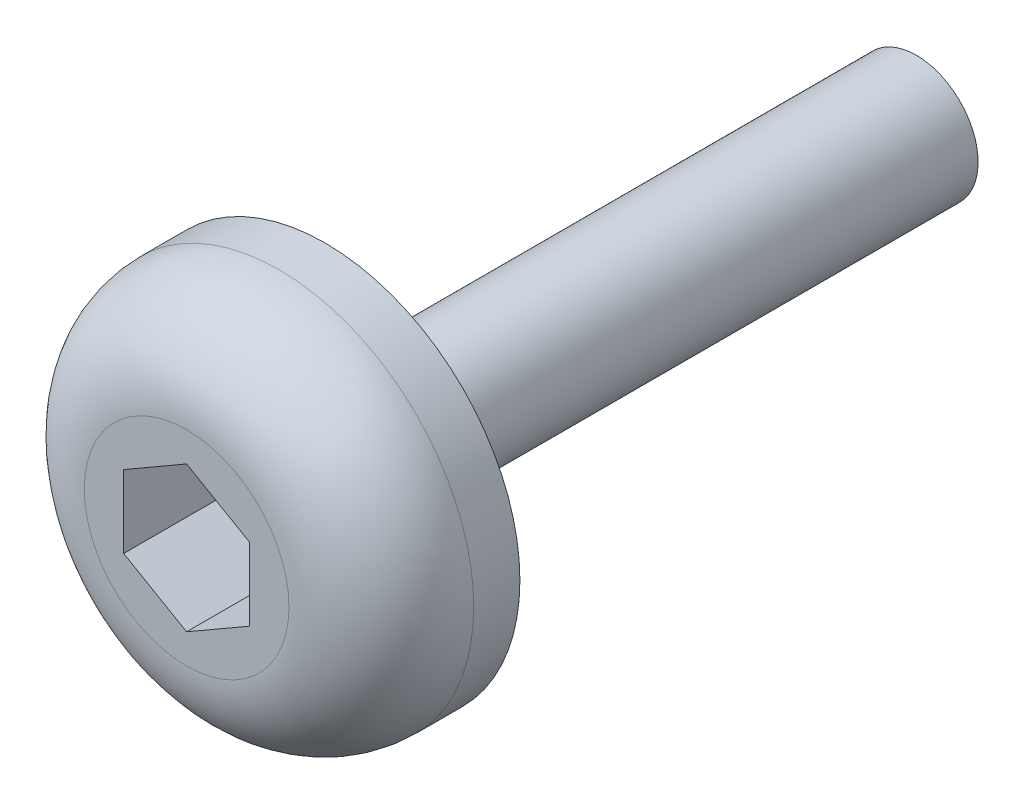
SolidWorks part; units mm, degrees
ref_plane "Front Plane" through (0, 0, 0) normal (0, 0, 1) x (1, 0, 0)
ref_plane "Top Plane" through (0, 0, 0) normal (0, 1, 0) x (1, 0, 0)
ref_plane "Right Plane" through (0, 0, 0) normal (1, 0, 0) x (0, 0, -1)
sketch "Sketch1" plane through (0, 0, 0) normal (0, 0, 1) x (1, 0, 0)
  circle A0 centre (0, 0) radius 5.3543
extrude "Boss-Extrude1" add sketch "Sketch1" along normal blind 3.81
fillet "Fillet1" radius 2.54 1 edges at (5.3543, 0, 3.81)
sketch "Sketch2" plane through (0, 0, 3.81) normal (0, 0, 1) x (1, 0, 0)
  line L1 (0, 1.9983) -> (-1.7306, 0.9992)
  line L2 (-1.7306, 0.9992) -> (-1.7306, -0.9992)
  line L3 (-1.7306, -0.9992) -> (0, -1.9983)
  line L4 (0, -1.9983) -> (1.7306, -0.9992)
  line L5 (1.7306, -0.9992) -> (1.7306, 0.9992)
  line L6 (1.7306, 0.9992) -> (0, 1.9983)
  circle A0 centre (0, 0) radius 1.7306 construction
extrude "Cut-Extrude1" cut sketch "Sketch2" against normal blind 2.794
sketch "Sketch3" plane through (0, 0, 0) normal (0, 0, -1) x (-1, 0, 0)
  circle A0 centre (0, 0) radius 1.697
extrude "Boss-Extrude2" add sketch "Sketch3" along normal blind 16.256
